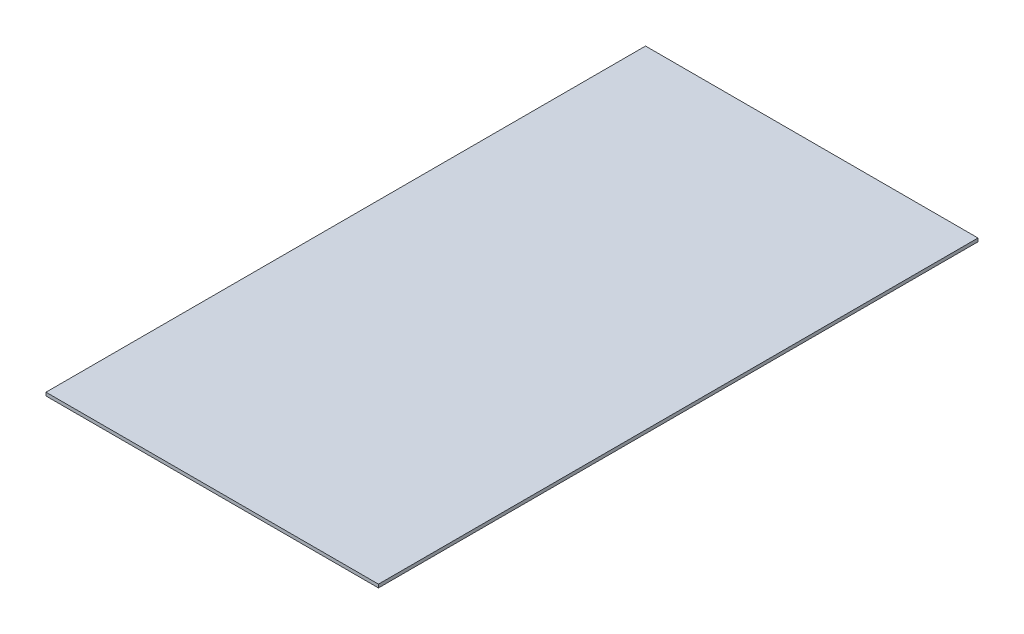
SolidWorks part; units mm, degrees
ref_plane "Front Plane" through (0, 0, 0) normal (0, 0, 1) x (1, 0, 0)
ref_plane "Top Plane" through (0, 0, 0) normal (0, 1, 0) x (1, 0, 0)
ref_plane "Right Plane" through (0, 0, 0) normal (1, 0, 0) x (0, 0, -1)
sketch "Sketch1" plane through (0, 0, 0) normal (0, 1, 0) x (1, 0, 0)
  line L1 (-150, 270.5) -> (150, 270.5)
  line L2 (-150, 270.5) -> (-150, -270.5)
  line L3 (-150, -270.5) -> (150, -270.5)
  line L4 (150, 270.5) -> (150, -270.5)
  line L5 (-150, 270.5) -> (150, -270.5) construction
  line L6 (-150, -270.5) -> (150, 270.5) construction
  point P0 (0, 0)
  dimension "D1" = 541
  dimension "D2" = 300
extrude "Boss-Extrude1" add sketch "Sketch1" along normal blind 3
